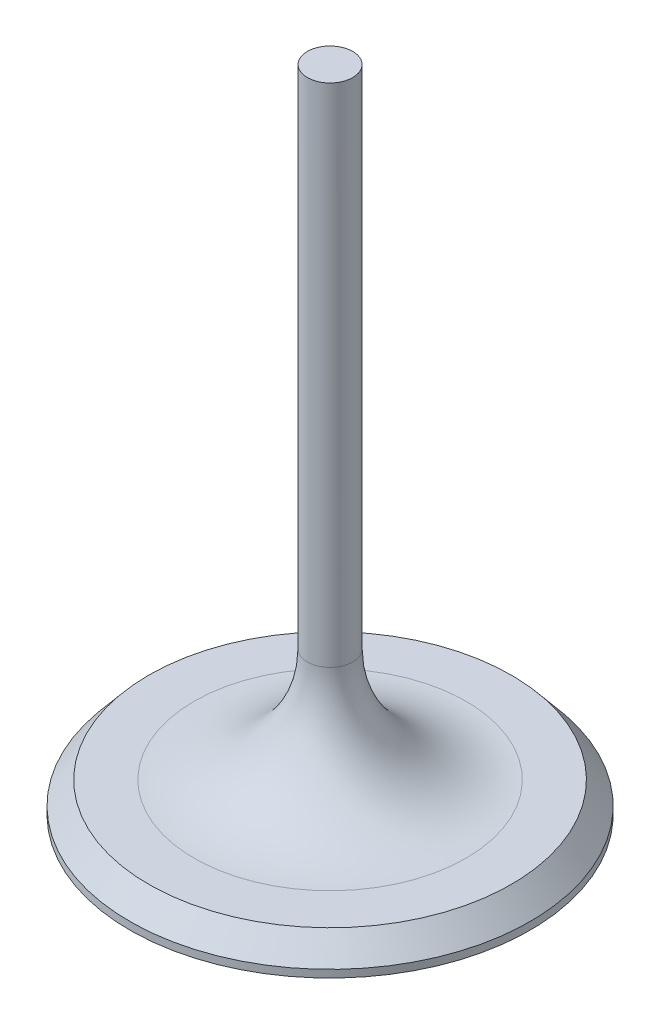
SolidWorks part; units mm, degrees
ref_plane "Front Plane" through (0, 0, 0) normal (0, 0, 1) x (1, 0, 0)
ref_plane "Top Plane" through (0, 0, 0) normal (0, 1, 0) x (1, 0, 0)
ref_plane "Right Plane" through (0, 0, 0) normal (1, 0, 0) x (0, 0, -1)
sketch "Sketch1" plane through (0, 0, 0) normal (0, 0, 1) x (1, 0, 0)
  line L0 (0, 72.0922) -> (0, -13.9078)
  line L1 (0, -13.9078) -> (26.5, -13.9078)
  line L2 (26.5, -13.9078) -> (26.5, -12.9078)
  line L3 (26.5, -12.9078) -> (24, -9.9078)
  line L4 (24, -9.9078) -> (18, -9.9078)
  line L5 (3, 5.0922) -> (3, 72.0922)
  line L6 (3, 72.0922) -> (0, 72.0922)
  line L7 (3, 5.0922) -> (3, -9.9078)
  line L8 (3, -9.9078) -> (18, -9.9078)
  dimension "D1" = 26.5
  dimension "D2" = 1
  dimension "D3" = 2.5
  dimension "D4" = 4
  dimension "D5" = 3
  dimension "D7" = 86
revolve "Revolve1" add sketch "Sketch1" angle 360 about L0
fillet "Fillet1" radius 15 1 edges at (-3, -9.9078, 0)
sketch "Sketch6" plane through (0, 72.0922, 0) normal (0, 1, 0) x (1, 0, 0)
  circle A0 centre (0, 0) radius 3
